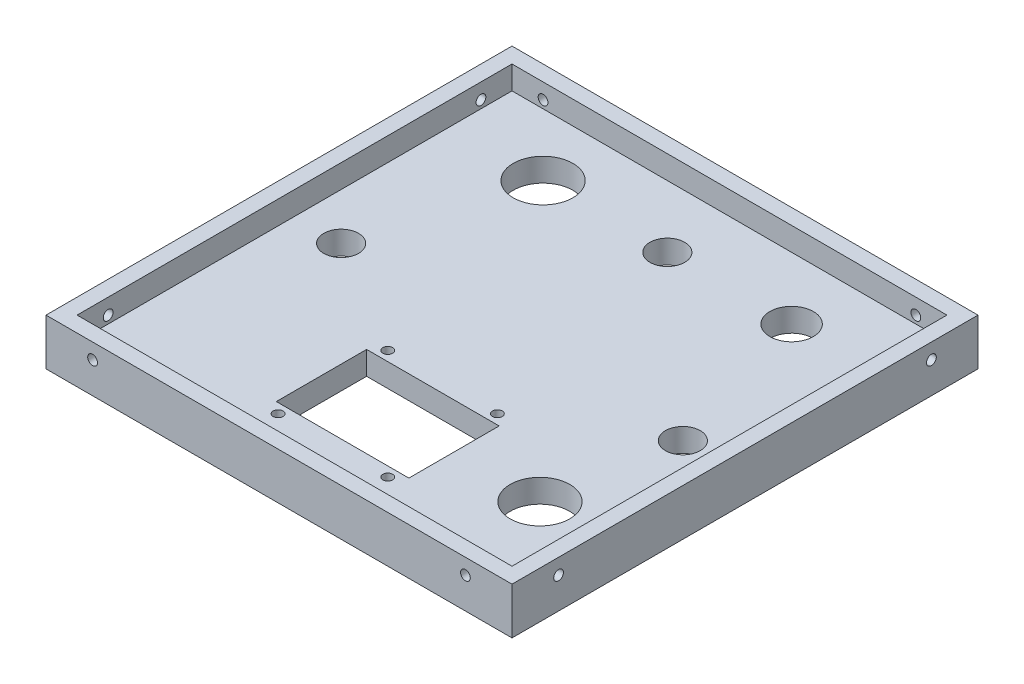
SolidWorks part; units mm, degrees
ref_plane "Front Plane" through (0, 0, 0) normal (0, 0, 1) x (1, 0, 0)
ref_plane "Top Plane" through (0, 0, 0) normal (0, 1, 0) x (1, 0, 0)
ref_plane "Right Plane" through (0, 0, 0) normal (1, 0, 0) x (0, 0, -1)
sketch "Sketch1" plane through (0, 0, 0) normal (0, 1, 0) x (1, 0, 0)
  line L1 (50.8, -50.8) -> (-50.8, -50.8)
  line L2 (50.8, -50.8) -> (50.8, 50.8)
  line L3 (50.8, 50.8) -> (-50.8, 50.8)
  line L4 (-50.8, -50.8) -> (-50.8, 50.8)
  line L5 (50.8, -50.8) -> (-50.8, 50.8) construction
  line L6 (50.8, 50.8) -> (-50.8, -50.8) construction
  point P0 (0, 0)
  dimension "D1" = 101.6
  dimension "D2" = 101.6
extrude "Boss-Extrude1" add sketch "Sketch1" along normal blind 3.175
sketch "Sketch2" plane through (0, 3.175, 0) normal (0, 1, 0) x (1, 0, 0)
  line L1 (-50.8, 50.8) -> (50.8, 50.8)
  line L2 (-50.8, 50.8) -> (-50.8, -50.8)
  line L3 (-50.8, -50.8) -> (50.8, -50.8)
  line L4 (50.8, 50.8) -> (50.8, -50.8)
  line L5 (-44.45, 44.45) -> (44.45, 44.45)
  line L6 (-44.45, 44.45) -> (-44.45, -44.45)
  line L7 (-44.45, -44.45) -> (44.45, -44.45)
  line L8 (44.45, 44.45) -> (44.45, -44.45)
  dimension "D1" = 6.35
  dimension "D2" = 6.35
  dimension "D3" = 6.35
extrude "Boss-Extrude2" add sketch "Sketch2" along normal blind 6.35
ref_axis "Axis1" through (0, 10.0012, 0) along (0, -1, 0)
sketch "Sketch3" plane through (0, 0, 50.8) normal (0, 0, 1) x (1, 0, 0)
  line L1 (-50.8, 9.525) -> (-50.8, 0) construction
  line L2 (-50.8, 9.525) -> (50.8, 9.525) construction
  line L4 (0, 0) -> (0, 9.525) construction
  line L5 (44.45, 9.525) -> (-44.45, 9.525) construction
  line L6 (-50.8, 0) -> (50.8, 0) construction
  circle A0 centre (-38.1, 6.35) radius 0.9995
  circle A2 centre (38.1, 6.35) radius 0.9995
  dimension "D3" = 1.999
  dimension "D1" = 12.7
  dimension "D2" = 3.175
  dimension "D4" = 6.35
extrude "Cut-Extrude1" cut sketch "Sketch3" against normal blind 6.35
pattern_circular "CirPattern1" count 4 over 360 about axis through (0, 10.0012, 0) along (0, -1, 0) of "Cut-Extrude1"
sketch "Sketch8" plane through (0, 3.175, 0) normal (0, 1, 0) x (1, 0, 0)
  line L1 (-44.45, 44.45) -> (44.45, 44.45)
  line L2 (-44.45, 44.45) -> (-44.45, -44.45)
  line L3 (-44.45, -44.45) -> (44.45, -44.45)
  line L4 (44.45, 44.45) -> (44.45, -44.45)
extrude "Boss-Extrude3" add sketch "Sketch8" along normal blind 1.5875
sketch "Sketch4" plane through (0, 0, 0) normal (0, 1, 0) x (1, 0, 0)
  line L1 (-50.8, 50.8) -> (50.8, 50.8)
  line L2 (-50.8, 50.8) -> (-50.8, -50.8)
  line L3 (-50.8, -50.8) -> (50.8, -50.8)
  line L4 (50.8, 50.8) -> (50.8, -50.8)
  line L5 (-47.625, 47.625) -> (47.625, 47.625)
  line L6 (-47.625, 47.625) -> (-47.625, -47.625)
  line L7 (-47.625, -47.625) -> (47.625, -47.625)
  line L8 (47.625, 47.625) -> (47.625, -47.625)
  dimension "D1" = 3.175
  dimension "D2" = 3.175
  dimension "D3" = 3.175
  dimension "D4" = 3.175
extrude "Cut-Extrude2" cut sketch "Sketch4" along normal through all
sketch "Sketch6" plane through (0, 0, 0) normal (0, -1, 0) x (1, 0, 0)
  line L0 (0, 0) -> (0, -31.75) construction
  line L1 (0, -31.75) -> (-25.4, -31.75) construction
  line L2 (0, -31.75) -> (25.4, -31.75) construction
  line L3 (47.625, 47.625) -> (47.625, -47.625) construction
  circle A0 centre (0, -31.75) radius 3.556
  circle A1 centre (-25.4, -31.75) radius 6.096
  circle A2 centre (25.4, -31.75) radius 4.445
  circle A5 centre (31.115, 25.4) radius 6.096
  dimension "D2" = 7.112
  dimension "D5" = 12.192
  dimension "D6" = 8.89
  dimension "D9" = 12.192
  dimension "D1" = 31.75
  dimension "D3" = 25.4
  dimension "D4" = 25.4
  dimension "D7" = 25.4
  dimension "D8" = 16.51
extrude "Inputs " cut sketch "Sketch6" against normal through all
sketch "Sketch5" plane through (0, 0, 0) normal (0, -1, 0) x (1, 0, 0)
  line L0 (0, 25.4) -> (0, 11.6501) construction
  line L1 (13.7499, 11.6501) -> (-13.7499, 11.6501) construction
  line L2 (13.7499, 11.6501) -> (13.7499, 39.1499) construction
  line L3 (13.7499, 39.1499) -> (-13.7499, 39.1499) construction
  line L4 (-13.7499, 11.6501) -> (-13.7499, 39.1499) construction
  line L5 (13.7499, 11.6501) -> (-13.7499, 39.1499) construction
  line L6 (13.7499, 39.1499) -> (-13.7499, 11.6501) construction
  line L7 (0, 25.4) -> (-13.7499, 25.4) construction
  line L8 (-47.625, 47.625) -> (47.625, 47.625) construction
  line L10 (13.5467, 16.1713) -> (-13.5467, 16.1713)
  line L11 (13.5467, 16.1713) -> (13.5467, 34.6287)
  line L12 (13.5467, 34.6287) -> (-13.5467, 34.6287)
  line L13 (-13.5467, 16.1713) -> (-13.5467, 34.6287)
  line L14 (13.5467, 16.1713) -> (-13.5467, 34.6287) construction
  line L15 (13.5467, 34.6287) -> (-13.5467, 16.1713) construction
  circle A0 centre (-11.2056, 14.1944) radius 0.9995
  circle A1 centre (11.2056, 14.1944) radius 0.9995
  circle A2 centre (11.2056, 36.6056) radius 0.9995
  circle A3 centre (-11.2056, 36.6056) radius 0.9995
  point P0 (0, 25.4)
  dimension "D5" = 1.999
  dimension "D1" = 25.4
  dimension "D2" = 27.4998
  dimension "D3" = 27.4998
  dimension "D4" = 8.4751
  dimension "D6" = 4.5212
  dimension "D7" = 0.4064
extrude "Screen" cut sketch "Sketch5" against normal through all
sketch "Sketch7" plane through (0, 0, 0) normal (0, -1, 0) x (1, 0, 0)
  line L0 (0, 0) -> (-34.925, 0) construction
  line L1 (0, 0) -> (34.925, 0) construction
  circle A0 centre (-34.925, 0) radius 3.556
  circle A1 centre (34.925, 0) radius 3.556
  dimension "D3" = 7.112
  dimension "D4" = 7.112
  dimension "D1" = 34.925
  dimension "D2" = 34.925
extrude "Cut-Extrude5" cut sketch "Sketch7" against normal through all
